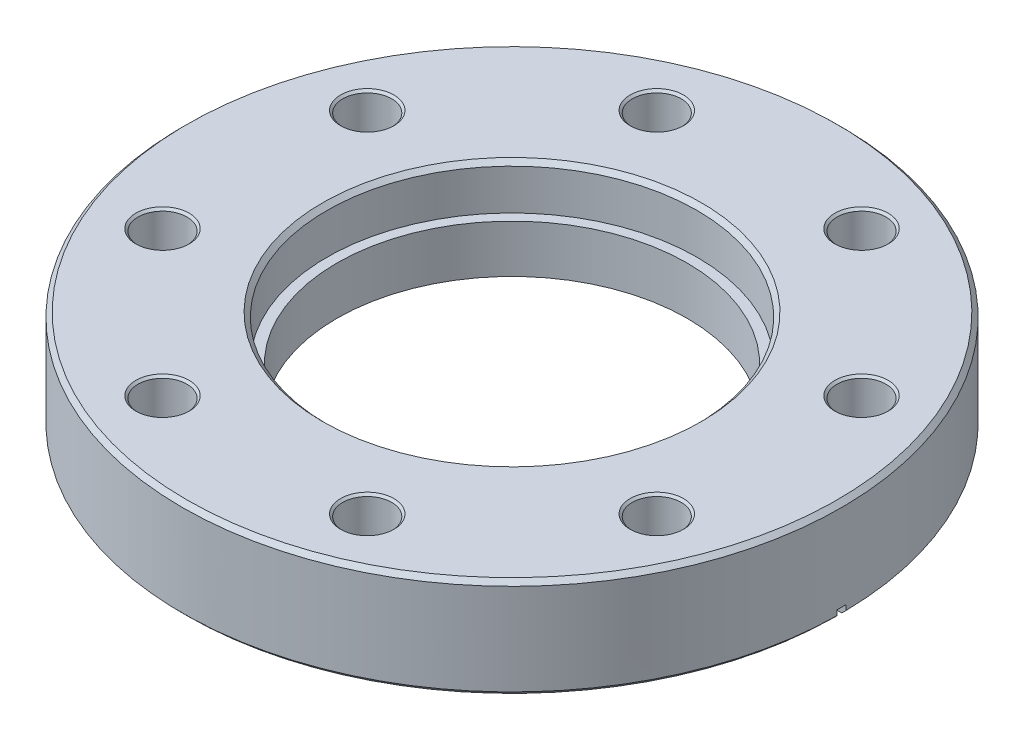
SolidWorks part; units mm, degrees
ref_plane "Front Plane" through (0, 0, 0) normal (0, 0, 1) x (1, 0, 0)
ref_plane "Top Plane" through (0, 0, 0) normal (0, 1, 0) x (1, 0, 0)
ref_plane "Right Plane" through (0, 0, 0) normal (1, 0, 0) x (0, 0, -1)
sketch "Sketch1" plane through (0, 0, 0) normal (0, 1, 0) x (1, 0, 0)
  circle A0 centre (0, 0) radius 56.769
  circle A1 centre (0, 0) radius 30.1625
  dimension "D1" = 113.538
  dimension "D2" = 60.325
extrude "Boss-Extrude1" add sketch "Sketch1" along normal blind 17.272
sketch "Sketch2" plane through (0, 17.272, 0) normal (0, 1, 0) x (1, 0, 0)
  circle A0 centre (0, 0) radius 31.877
  dimension "D1" = 63.754
extrude "Cut-Extrude1" cut sketch "Sketch2" against normal blind 7.747
chamfer "Chamfer1" distance 0.762 angle 45 3 edges at (0, 0, 56.769) (0, 17.272, 56.769) (0, 17.272, 31.877)
sketch "Sketch5" plane through (0, 0, 0) normal (0, 0, 1) x (1, 0, 0)
  line L0 (-41.275, 0) -> (-41.275, 1.6256)
  line L1 (-41.275, 1.6256) -> (-38.608, 0.6604)
  line L2 (-38.608, 0.6604) -> (-38.608, 1.27)
  line L3 (-38.608, 1.27) -> (0, 1.27)
  line L4 (0, 1.27) -> (0, 0)
  line L5 (0, 0) -> (-41.275, 0)
  dimension "D1" = 41.275
  dimension "D2" = 1.6256
  dimension "D3" = 1.27
  dimension "D4" = 38.608
  dimension "D5" = 0.6096
revolve "Cut-Revolve1" cut sketch "Sketch5" angle 360 about axis through (0, 17.272, 0) along (0, -1, 0)
sketch "Sketch4" plane through (0, 17.272, 0) normal (0, 1, 0) x (1, 0, 0)
  line L0 (0, 56.007) -> (0, 0) construction
  line L1 (0, 0) -> (-17.6324, 42.5683) construction
  circle A0 centre (-17.6324, 42.5683) radius 4.2164
  circle A1 centre (0, 0) radius 56.007 construction
  dimension "D1" = 8.4328
  dimension "D2" = 46.0756
  dimension "D3" = 22.5
extrude "Cut-Extrude2" cut sketch "Sketch4" against normal through all
chamfer "Chamfer2" distance 0.381 angle 45 2 edges at (-17.6324, 0, -38.3519) (-17.6324, 17.272, -38.3519)
pattern_circular "CirPattern1" count 8 every 45 about axis through (0, 0, 0) along (0, 1, 0) of "Cut-Extrude2", "Chamfer2"
sketch "Sketch6" plane through (0, 0, 0) normal (0, 0, 1) x (1, 0, 0)
  line L0 (-40.64, 0.9331) -> (-56.769, 1.7784)
  line L1 (-56.769, 16.51) -> (-56.769, 0.762) construction
  line L2 (-56.769, 1.7784) -> (-56.769, -1.1967)
  line L3 (-56.769, -1.1967) -> (-40.64, -1.1967)
  line L4 (56.769, 1.6453) -> (56.769, -1.1967)
  line L5 (56.769, 0.762) -> (56.769, 16.51) construction
  line L6 (56.769, -1.1967) -> (40.64, -1.1967)
  line L7 (56.769, 1.6453) -> (40.64, 0.8)
  line L8 (-40.64, 0.9331) -> (-40.64, -1.1967)
  line L9 (40.64, 0.8) -> (40.64, -1.1967)
  line L10 (-40.64, 0.9331) -> (0, -1.1967) construction
  line L11 (-40.64, -1.1967) -> (40.64, -1.1967) construction
  line L12 (40.64, 0.8) -> (0, -1.1967) construction
  dimension "D1" = 40.64
  dimension "D2" = 3
  dimension "D3" = 3
  dimension "D4" = 40.64
extrude "Cut-Extrude3" cut sketch "Sketch6" against normal mid plane 1.5875
